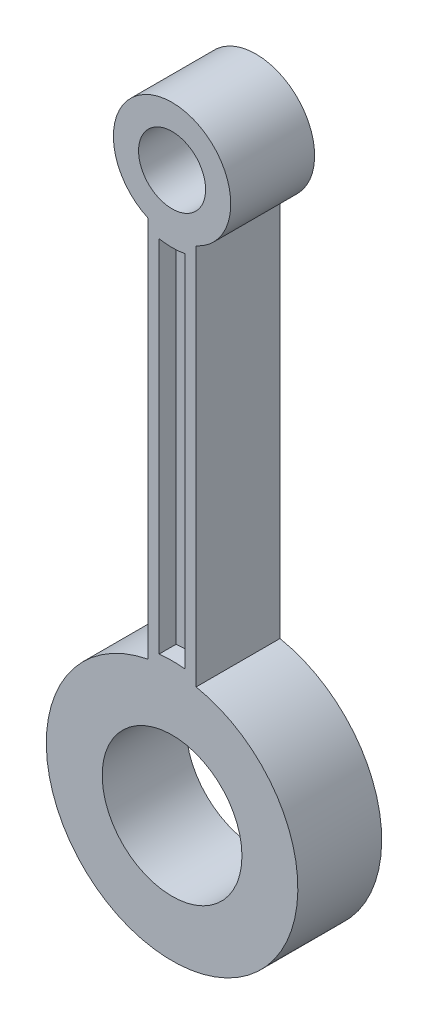
SolidWorks part; units mm, degrees
ref_plane "Ön Düzlem" through (0, 0, 0) normal (0, 0, 1) x (1, 0, 0)
ref_plane "Üst Düzlem" through (0, 0, 0) normal (0, 1, 0) x (1, 0, 0)
ref_plane "Sağ Düzlem" through (0, 0, 0) normal (1, 0, 0) x (0, 0, -1)
sketch "Sketch1" plane through (0, 0, 0) normal (0, 0, 1) x (1, 0, 0)
  line L0 (-4.5894, 56.7607) -> (-4.5894, -7.5723)
  line L4 (2.0106, -9.3765) -> (2.0106, 58.9591)
  line L6 (-6.5894, 58.9591) -> (-6.5894, -9.3765)
  line L8 (0.0106, -9.3765) -> (0.0106, 58.9591) construction
  line L10 (2.0106, 60.9591) -> (-6.5894, 60.9591) construction
  line L12 (2.0106, -11.3765) -> (2.0106, 60.9591) construction
  line L13 (-6.5894, -11.3765) -> (2.0106, -11.3765) construction
  line L14 (-6.5894, 60.9591) -> (-6.5894, -11.3765) construction
  line L15 (0.0106, 58.9591) -> (-4.5894, 58.9591) construction
  line L16 (0.0106, -7.5723) -> (0.0106, 56.7607)
  line L17 (-4.5894, 58.9591) -> (-4.5894, -9.3765) construction
  line L18 (-4.5894, -9.3765) -> (0.0106, -9.3765) construction
  arc A0 (2.0106, 58.9591) -> (-6.5894, 58.9591) centre (-2.2894, 68.5382) ccw
  arc A1 (-4.5894, 56.7607) -> (0.0106, 56.7607) centre (-2.2894, 68.5382) ccw
  arc A2 (0.0106, -7.5723) -> (-4.5894, -7.5723) centre (-2.2894, -31.4618) ccw
  circle A3 centre (-2.2894, -31.4618) radius 12.5
  circle A4 centre (-2.2894, 68.5382) radius 6
  arc A5 (-6.5894, -9.3765) -> (2.0106, -9.3765) centre (-2.2894, -31.4618) ccw
  dimension "D1" = 24
  dimension "D2" = 21
  dimension "D3" = 48
  dimension "D4" = 25
  dimension "D8" = 45
  dimension "D7" = 100
  dimension "D6" = 2
extrude "Boss-Extrude2" add sketch "Sketch1" along normal mid plane 15
sketch "Sketch2" plane through (0, 0, 0) normal (0, 0, 1) x (1, 0, 0)
  line L0 (-4.5894, 56.7607) -> (-4.5894, -7.5723) construction
  line L1 (0.0106, -7.5723) -> (0.0106, 56.7607) construction
  line L2 (-4.5894, 56.7607) -> (-4.5894, -7.5723)
  line L3 (0.0106, -7.5723) -> (0.0106, 56.7607)
  arc A0 (0.0106, -7.5723) -> (-4.5894, -7.5723) centre (-2.2894, -31.4618) ccw construction
  arc A1 (-4.5894, 56.7607) -> (0.0106, 56.7607) centre (-2.2894, 68.5382) ccw construction
  arc A2 (0.0106, -7.5723) -> (-4.5894, -7.5723) centre (-2.2894, -31.4618) ccw
  arc A3 (-4.5894, 56.7607) -> (0.0106, 56.7607) centre (-2.2894, 68.5382) ccw
extrude "Boss-Extrude3" add sketch "Sketch2" along normal mid plane 9
